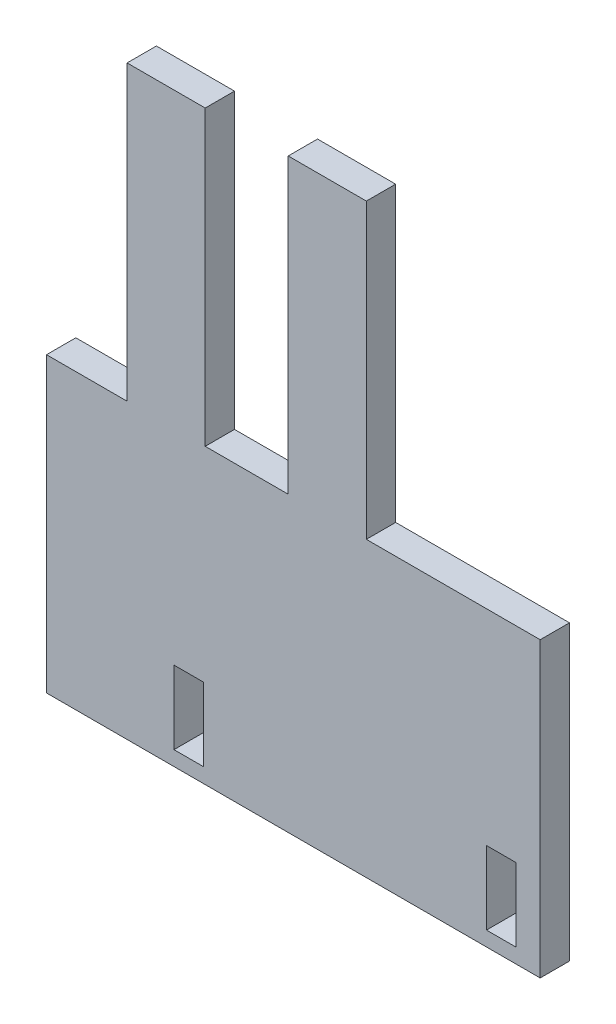
SolidWorks part; units mm, degrees
ref_plane "Plan de face" through (0, 0, 0) normal (0, 0, 1) x (1, 0, 0)
ref_plane "Plan de dessus" through (0, 0, 0) normal (0, 1, 0) x (1, 0, 0)
ref_plane "Plan de droite" through (0, 0, 0) normal (1, 0, 0) x (0, 0, -1)
sketch "Esquisse1" plane through (0, 0, 0) normal (0, 0, 1) x (1, 0, 0)
  line L0 (42.1676, -72.6187) -> (42.1676, -12.6187)
  line L1 (42.1676, -12.6187) -> (6.5676, -12.6187)
  line L2 (6.5676, -12.6187) -> (6.5676, 47.3813)
  line L3 (-58.9324, -72.6187) -> (42.1676, -72.6187)
  line L4 (6.5676, 47.3813) -> (-9.4324, 47.3813)
  line L5 (37.1676, -54.6187) -> (31.1676, -54.6187)
  line L6 (37.1676, -54.6187) -> (37.1676, -69.6187)
  line L7 (37.1676, -69.6187) -> (31.1676, -69.6187)
  line L8 (31.1676, -54.6187) -> (31.1676, -69.6187)
  line L9 (-26.8324, -54.6187) -> (-32.8324, -54.6187)
  line L10 (-26.8324, -54.6187) -> (-26.8324, -69.6187)
  line L11 (-26.8324, -69.6187) -> (-32.8324, -69.6187)
  line L12 (-32.8324, -54.6187) -> (-32.8324, -69.6187)
  line L13 (-9.4324, 47.3813) -> (-9.4324, -12.6187)
  line L14 (-9.4324, -12.6187) -> (-26.4324, -12.6187)
  line L15 (-26.4324, -12.6187) -> (-26.4324, 47.3813)
  line L16 (-26.4324, 47.3813) -> (-42.4324, 47.3813)
  line L17 (-42.4324, 47.3813) -> (-42.4324, -12.6187)
  line L18 (-42.4324, -12.6187) -> (-58.9324, -12.6187)
  line L19 (-58.9324, -12.6187) -> (-58.9324, -72.6187)
  dimension "D2" = 120
  dimension "D3" = 6
  dimension "D4" = 15
  dimension "D5" = 6
  dimension "D6" = 15
  dimension "D7" = 101.1
  dimension "D8" = 58
  dimension "D9" = 3
  dimension "D10" = 3
  dimension "D11" = 16
  dimension "D12" = 16.5
  dimension "D13" = 16
  dimension "D14" = 17
  dimension "D15" = 60
  dimension "D16" = 60
  dimension "D17" = 60
  dimension "D18" = 60
  dimension "D19" = 5
extrude "Boss.-Extru.1" add sketch "Esquisse1" along normal blind 6
